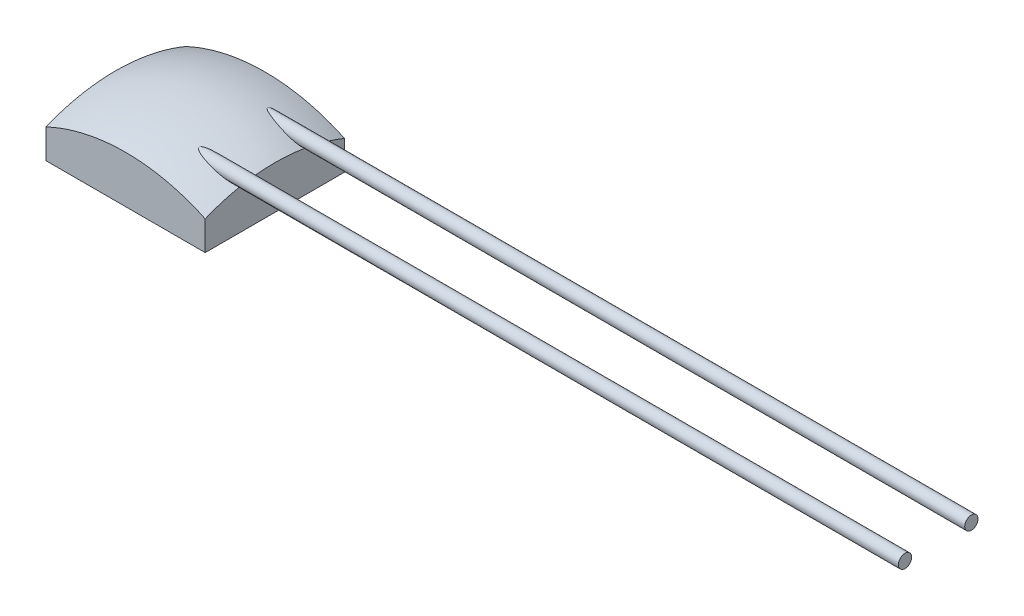
SolidWorks part; units mm, degrees
material "Керамика фарфор"
ref_plane "Front" through (0, 0, 0) normal (0, 0, 1) x (1, 0, 0)
ref_plane "Top" through (0, 0, 0) normal (0, 1, 0) x (1, 0, 0)
ref_plane "Right" through (0, 0, 0) normal (1, 0, 0) x (0, 0, -1)
sketch "Эскиз2" plane through (0, 0, 0) normal (0, 0, 1) x (1, 0, 0)
  line L0 (0, 0) -> (1.75, 0)
  line L1 (1.75, 0) -> (1.75, 0.3367)
  line L2 (0, 0.9) -> (0.9272, 0.9) construction
  line L3 (0, 0) -> (0, 0.9) construction
  line L4 (0, 0) -> (0, 0.9)
  arc A0 (1.75, 0.3367) -> (0, 0.9) centre (0, -2.1) ccw
  dimension "D3" = 3
  dimension "D1" = 0.9
  dimension "D2" = 3.5
revolve "Повернуть1" add sketch "Эскиз2" angle 360 about L4
sketch "Эскиз3" plane through (0, 0, 0) normal (0, -1, 0) x (1, 0, 0)
  line L1 (-1.2, -1.05) -> (1.2, -1.05)
  line L2 (-1.2, -1.05) -> (-1.2, 1.05)
  line L3 (-1.2, 1.05) -> (1.2, 1.05)
  line L4 (1.2, -1.05) -> (1.2, 1.05)
  line L5 (-1.2, -1.05) -> (1.2, 1.05) construction
  line L6 (-1.2, 1.05) -> (1.2, -1.05) construction
  point P0 (0, 0)
  dimension "D1" = 2.1
  dimension "D2" = 2.4
extrude "Вырез-Вытянуть1" cut sketch "Эскиз3" against normal through all flip side to cut
sketch "Эскиз4" plane through (1.2, 0, 0) normal (1, 0, 0) x (0, 0, -1)
  line L0 (1.05, 0) -> (-1.05, 0) construction
  circle A0 centre (-0.5, 0.7) radius 0.1
  circle A1 centre (0.5, 0.7) radius 0.1
  dimension "D1" = 0.2
  dimension "D2" = 1
  dimension "D3" = 0.5
  dimension "D4" = 0.7
extrude "Бобышка-Вытянуть2" add sketch "Эскиз4" along normal blind 10 and the other way blind 1
